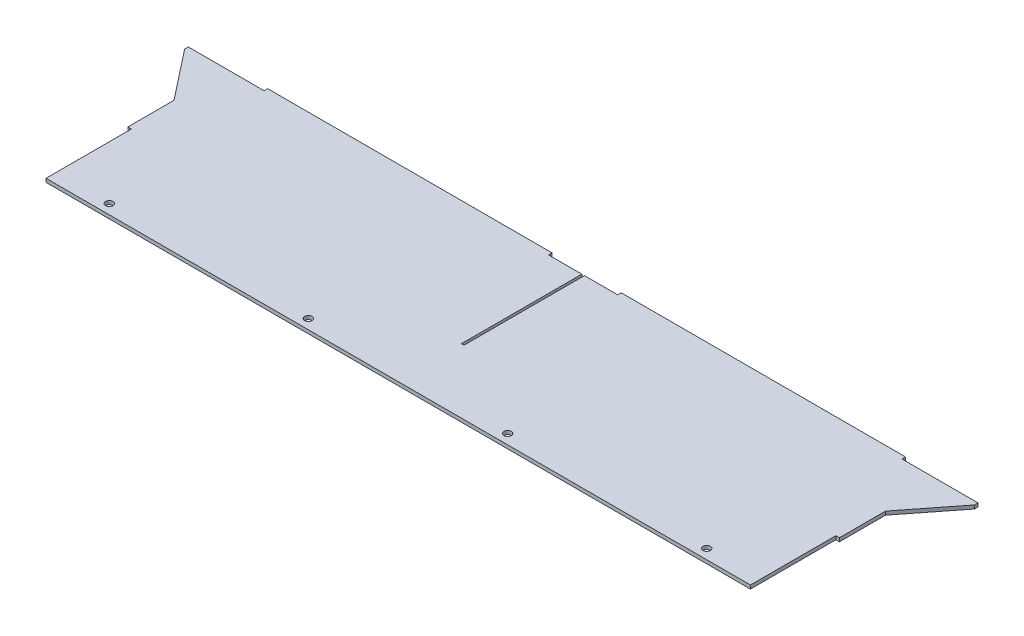
SolidWorks part; units mm, degrees
material "6061-T6 (SS)"
ref_plane "X-Y Datum" through (0, 0, 0) normal (0, 0, 1) x (1, 0, 0)
ref_plane "X-Z Datum" through (0, 0, 0) normal (0, 1, 0) x (1, 0, 0)
ref_plane "Y-Z Datum" through (0, 0, 0) normal (1, 0, 0) x (0, 0, -1)
sketch "Sketch1" plane through (0, 0, 0) normal (0, 1, 0) x (1, 0, 0)
  line L1 (-317.6778, 82.55) -> (317.6778, 82.55)
  line L2 (-317.6778, 82.55) -> (-317.6778, -82.55)
  line L3 (-317.6778, -82.55) -> (317.6778, -82.55)
  line L4 (317.6778, 82.55) -> (317.6778, -82.55)
  line L5 (-317.6778, 82.55) -> (317.6778, -82.55) construction
  line L6 (-317.6778, -82.55) -> (317.6778, 82.55) construction
  point P0 (0, 0)
  dimension "D1" = 635.3556
  dimension "D2" = 165.1
extrude "Boss-Extrude1" add sketch "Sketch1" along normal mid plane 3.175
sketch "Sketch2" plane through (0, 0, -82.55) normal (0, 0, -1) x (-1, 0, 0)
  line L20 (-317.6778, -1.5875) -> (317.6778, -1.5875) construction
  line L21 (-284.8229, -1.5875) -> (-30.8229, -1.5875)
  line L22 (30.8229, -1.5875) -> (284.8229, -1.5875)
  line L40 (30.8229, -1.5875) -> (30.8229, 1.5875)
  line L41 (30.8229, 1.5875) -> (284.8229, 1.5875)
  line L42 (284.8229, 1.5875) -> (284.8229, -1.5875)
  line L56 (-284.8229, -1.5875) -> (-284.8229, 1.5875)
  line L57 (-284.8229, 1.5875) -> (-30.8229, 1.5875)
  line L58 (-30.8229, 1.5875) -> (-30.8229, -1.5875)
extrude "Boss-Extrude2" add sketch "Sketch2" along normal blind 3.175
sketch "Sketch3" plane through (0, -1.5875, 0) normal (0, -1, 0) x (1, 0, 0)
  line L0 (317.6778, -82.55) -> (352.6028, -82.55)
  line L1 (352.6028, -82.55) -> (352.6028, -79.375)
  line L3 (352.6028, -79.375) -> (317.6778, -34.925)
  line L4 (317.6778, 82.55) -> (317.6778, -82.55) construction
  line L17 (317.6778, -82.55) -> (317.6778, 82.55)
  line L18 (317.6778, 82.55) -> (-317.6778, 82.55)
  line L19 (-317.6778, 82.55) -> (-317.6778, -82.55)
  line L20 (-317.6778, -82.55) -> (-284.8229, -82.55)
  line L21 (-284.8229, -82.55) -> (-284.8229, -85.725)
  line L22 (-284.8229, -85.725) -> (-30.8229, -85.725)
  line L23 (-30.8229, -85.725) -> (-30.8229, -82.55)
  line L24 (-30.8229, -82.55) -> (30.8229, -82.55)
  line L25 (30.8229, -82.55) -> (30.8229, -85.725)
  line L26 (30.8229, -85.725) -> (284.8229, -85.725)
  line L27 (284.8229, -85.725) -> (284.8229, -82.55)
  line L28 (284.8229, -82.55) -> (317.6778, -82.55)
  line L29 (317.6778, -82.55) -> (317.6778, -34.925)
  dimension "D1" = 34.925
  dimension "D2" = 3.175
  dimension "D3" = 44.45
  dimension "D4" = 0
extrude "Boss-Extrude3" add sketch "Sketch3" against normal blind 3.175
mirror "Mirror1" about plane through (0, 0, 0) normal (1, 0, 0) of "Boss-Extrude3"
sketch "Sketch4" plane through (0, -1.5875, 0) normal (0, -1, 0) x (1, 0, 0)
  line L0 (-284.4038, 82.55) -> (-284.4038, 71.882)
  line L1 (-317.6778, 82.55) -> (317.6778, 82.55) construction
  line L2 (-284.4038, 71.882) -> (-317.6778, 71.882)
  line L3 (-317.6778, -34.925) -> (-317.6778, 82.55) construction
  circle A0 centre (-284.4038, 71.882) radius 3.675
extrude "Cut-Extrude1" [suppressed] cut sketch "Sketch4" against normal through all contours L2 A0 L0 | L0 A0 L2
pattern_linear "LPattern1" [suppressed] count 5 spacing 139.7
sketch "Sketch5" plane through (0, -1.5875, 0) normal (0, -1, 0) x (1, 0, 0)
  line L0 (-317.6778, 82.55) -> (317.6778, 82.55) construction
  line L1 (-317.6778, -34.925) -> (-317.6778, 82.55) construction
  line L2 (-317.6778, 82.55) -> (317.6778, 82.55)
  line L3 (-317.6778, -34.925) -> (-317.6778, 82.55)
  line L4 (0, 127.4245) -> (0, -127.4245) construction
  line L5 (-317.6778, 82.55) -> (-314.5028, 82.55)
  line L6 (-317.6778, 82.55) -> (-317.6778, 6.35)
  line L7 (-317.6778, 6.35) -> (-314.5028, 6.35)
  line L8 (-314.5028, 82.55) -> (-314.5028, 6.35)
  line L9 (317.6778, 6.35) -> (314.5028, 6.35)
  line L10 (314.5028, 82.55) -> (314.5028, 6.35)
  line L11 (317.6778, -34.925) -> (317.6778, 82.55)
  line L12 (30.8229, -82.55) -> (-30.8229, -82.55) construction
  line L13 (30.8229, -82.55) -> (-30.8229, -82.55)
  line L14 (-1.143, -85.725) -> (-1.143, -82.55) construction
  line L15 (-1.143, -85.725) -> (-1.143, -82.55)
  line L17 (-1.143, -82.55) -> (1.143, -82.55)
  line L18 (-1.143, -82.55) -> (-1.143, 24.892)
  line L19 (-1.143, 24.892) -> (1.143, 24.892)
  line L20 (1.143, -82.55) -> (1.143, 24.892)
  point P10 (0, 0)
  line M10 (317.6778, -34.925) -> (317.6778, 82.55)
  line M11 (317.6778, 82.55) -> (-317.6778, 82.55)
  line M12 (-317.6778, 82.55) -> (-317.6778, -34.925)
  dimension "D1" = 3.175
  dimension "D2" = 76.2
  dimension "D3" = 2.286
  dimension "D4" = 107.442
extrude "Cut-Extrude2" cut sketch "Sketch5" against normal through all contours L19 L4 L17 L20 | L4 L19 L18 L13 | L8 L2 L7 M12 | L10 L9 M11 M10
sketch "Sketch6" plane through (0, -1.5875, 0) normal (0, -1, 0) x (1, 0, 0)
  line L0 (-314.5028, 82.55) -> (314.5028, 82.55) construction
  line L1 (-314.5028, 82.55) -> (314.5028, 82.55)
  line L2 (0, 127.6954) -> (0, 37.4046) construction
  line L3 (314.5028, 82.55) -> (314.5028, 6.35) construction
  circle A0 centre (266.7, 73.8124) radius 3
  point P6 (0, 82.55)
  dimension "D1" = 6
  dimension "D2" = 8.7376
  dimension "D3" = 47.8028
hole_wizard "M6 Clearance Hole1" positions "Sketch7" profile "Sketch8" hole size "M6" standard "ANSI Metric" end condition through all
sketch "Sketch7" plane through (0, 1.5875, 0) normal (0, 1, 0) x (1, 0, 0)
  point P0 (266.7, -73.8124)
sketch "Sketch8" plane through (266.7, 1.5875, 73.8124) normal (1, 0, 0) x (0, 0, 1)
  line L0 (0, 0) -> (0, 3.175)
  line L1 (0, 3.175) -> (3.3, 3.175)
  line L2 (3.3, 3.175) -> (3.3, 0)
  line L5 (3.3, 0) -> (0, 0)
  line L11 (0, -6.35) -> (0, 107.95) construction
  dimension "Thru Hole Dia." = 6.6
  dimension "Thru Hole Depth" = 3.175
pattern_linear "LPattern2" count 4 spacing 177.8 along (-1, 0, 0) of "M6 Clearance Hole1"
